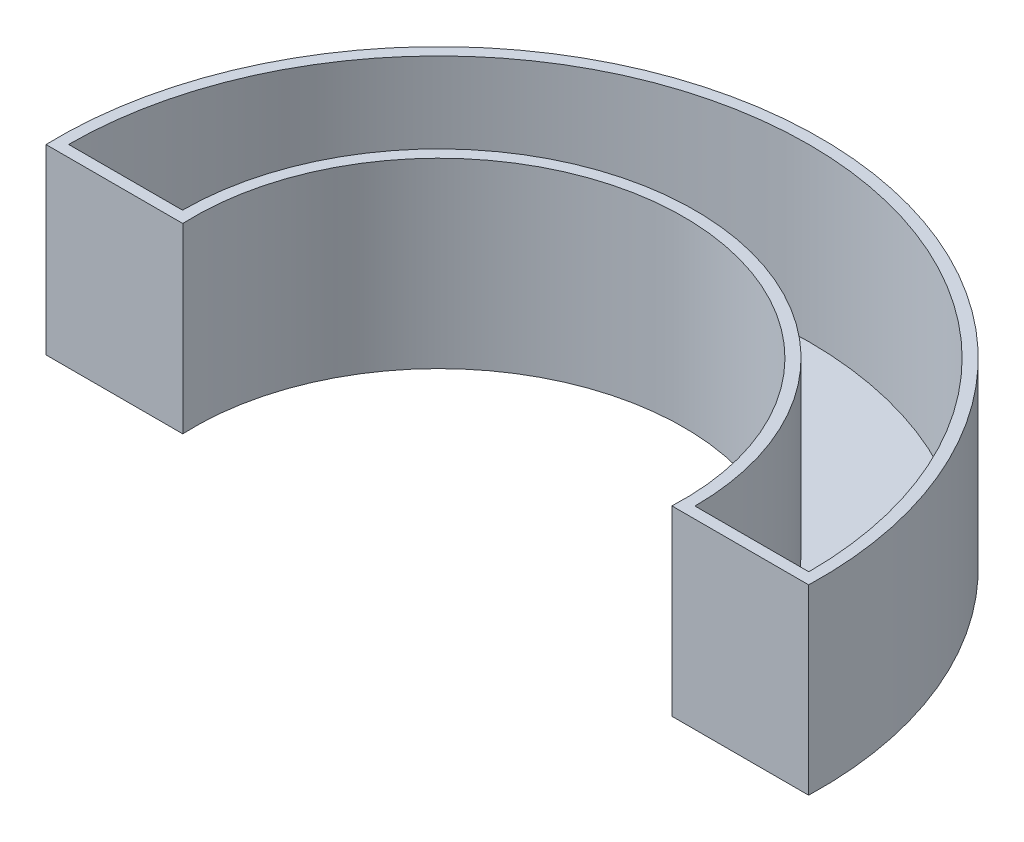
SolidWorks part; units mm, degrees
ref_plane "Front Plane" through (0, 0, 0) normal (0, 0, 1) x (1, 0, 0)
ref_plane "Top Plane" through (0, 0, 0) normal (0, 1, 0) x (1, 0, 0)
ref_plane "Right Plane" through (0, 0, 0) normal (1, 0, 0) x (0, 0, -1)
sketch "Sketch1" plane through (0, 0, 0) normal (0, 1, 0) x (1, 0, 0)
  line L0 (-13, 0) -> (-9, 0)
  line L1 (9, 0) -> (13, 0)
  circle A0 centre (0, 0) radius 12.43 construction
  circle A1 centre (0, 0) radius 9.43 construction
  circle A2 centre (0, 0) radius 13 construction
  circle A3 centre (0, 0) radius 9 construction
  arc A4 (9, 0) -> (-9, 0) centre (0, 0) ccw
  arc A5 (13, 0) -> (-13, 0) centre (0, 0) ccw
  dimension "D1" = 18.86
  dimension "D2" = 24.86
  dimension "D3" = 26
  dimension "D4" = 18
sketch "Sketch3" plane through (0, 0, 0) normal (0, 1, 0) x (1, 0, 0)
  line L5 (9, 0) -> (13, 0) construction
  line L6 (-13, 0) -> (-9, 0) construction
  line L7 (8.5907, -0.4) -> (13.394, -0.4)
  line L8 (-13.394, -0.4) -> (-8.5907, -0.4)
  line L9 (8.5907, -0.4) -> (13.394, -0.4)
  line L10 (-13.394, -0.4) -> (-8.5907, -0.4)
  line L11 (9, 0) -> (13, 0)
  line L12 (-13, 0) -> (-9, 0)
  arc A5 (13, 0) -> (-13, 0) centre (0, 0) ccw construction
  arc A6 (9, 0) -> (-9, 0) centre (0, 0) ccw construction
  arc A7 (13.394, -0.4) -> (-13.394, -0.4) centre (0, 0) ccw
  arc A8 (8.5907, -0.4) -> (-8.5907, -0.4) centre (0, 0) ccw
  arc A9 (13.394, -0.4) -> (-13.394, -0.4) centre (0, 0) ccw
  arc A10 (8.5907, -0.4) -> (-8.5907, -0.4) centre (0, 0) ccw
  arc A11 (13, 0) -> (-13, 0) centre (0, 0) ccw
  arc A12 (9, 0) -> (-9, 0) centre (0, 0) ccw
  dimension "D1" = 0.4
extrude "Boss-Extrude1" add sketch "Sketch3" along normal blind 6
sketch "Sketch4" plane through (0, 0, 0) normal (0, -1, 0) x (1, 0, 0)
  line L0 (8.5907, 0.4) -> (13.394, 0.4) construction
  line L1 (-13.394, 0.4) -> (-8.5907, 0.4) construction
  line L2 (8.5907, 0.4) -> (13.394, 0.4)
  line L3 (-13.394, 0.4) -> (-8.5907, 0.4)
  arc A0 (-13.394, 0.4) -> (13.394, 0.4) centre (0, 0) ccw construction
  arc A1 (-8.5907, 0.4) -> (8.5907, 0.4) centre (0, 0) ccw construction
  arc A2 (-13.394, 0.4) -> (13.394, 0.4) centre (0, 0) ccw
  arc A3 (-8.5907, 0.4) -> (8.5907, 0.4) centre (0, 0) ccw
extrude "Boss-Extrude2" add sketch "Sketch4" along normal blind 0.4
